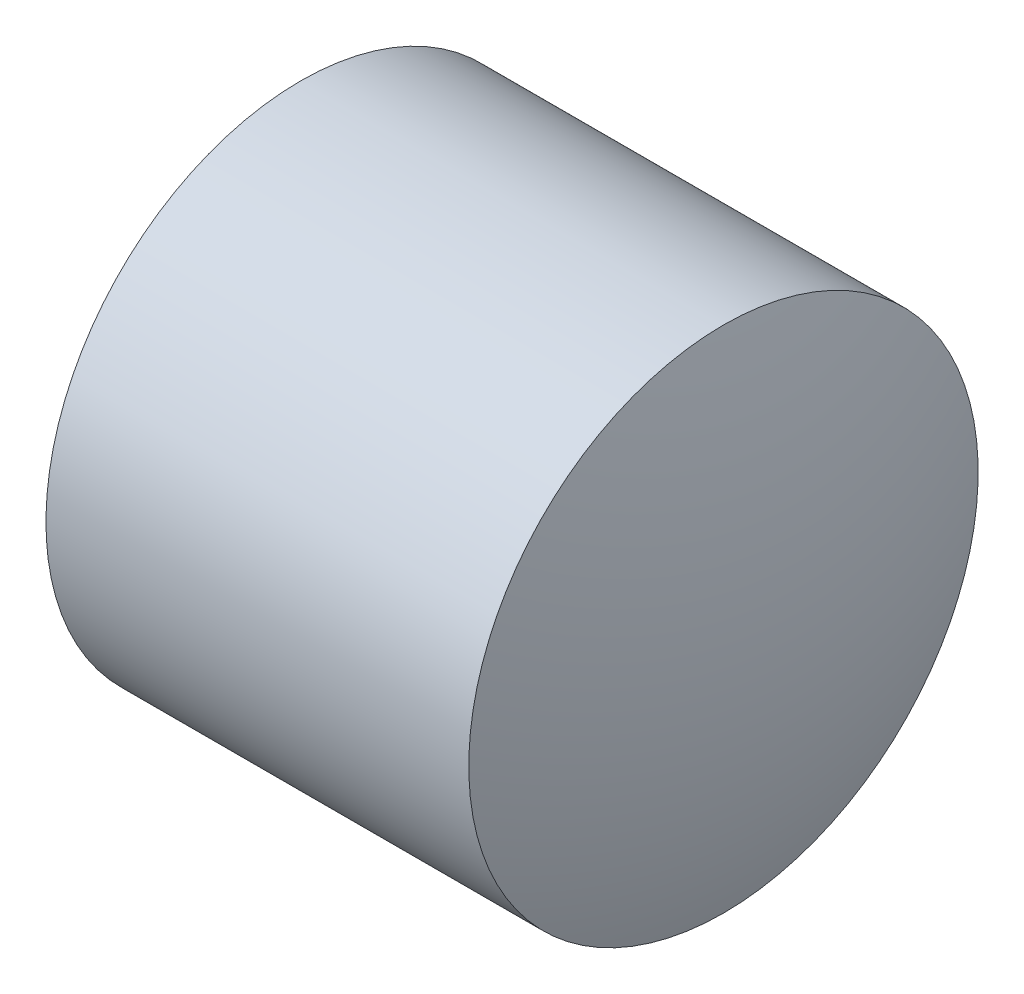
SolidWorks part; units mm, degrees
ref_plane "前视基准面" through (0, 0, 0) normal (0, 0, 1) x (1, 0, 0)
ref_plane "上视基准面" through (0, 0, 0) normal (0, 1, 0) x (1, 0, 0)
ref_plane "右视基准面" through (0, 0, 0) normal (1, 0, 0) x (0, 0, -1)
sketch "草图2" plane through (0, 0, 0) normal (0, 0, 1) x (1, 0, 0)
  line L0 (17.9332, 14.4841) -> (22.9132, 14.4841)
  line L2 (22.9132, 8.4841) -> (17.9332, 8.4841)
  line L4 (23.7753, 11.4841) -> (17.0465, 11.4841) construction
  arc A0 (17.9332, 14.4841) -> (17.9332, 8.4841) centre (26.5019, 11.4841) ccw
  arc A1 (22.9132, 8.4841) -> (22.9132, 14.4841) centre (14.3445, 11.4841) ccw
  dimension "D1" = 4.98
  dimension "D2" = 6
revolve "旋转1" add sketch "草图2" angle 360 about L4
